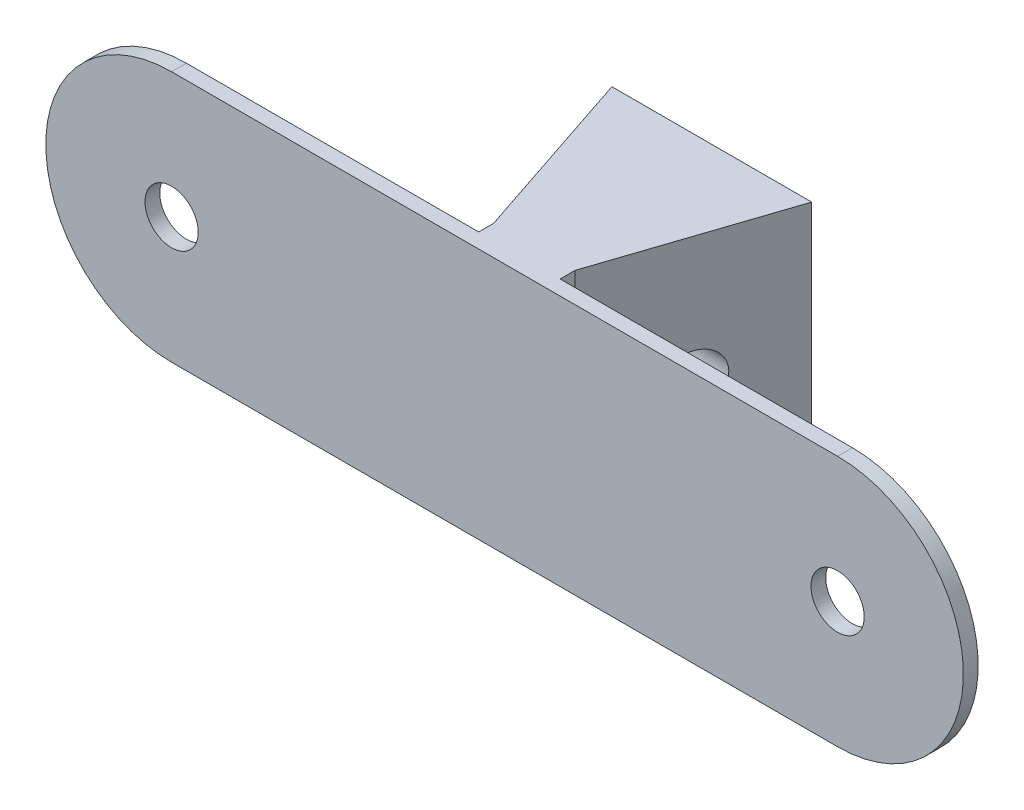
SolidWorks part; units mm, degrees
ref_plane "Front Plane" through (0, 0, 0) normal (0, 0, 1) x (1, 0, 0)
ref_plane "Top Plane" through (0, 0, 0) normal (0, 1, 0) x (1, 0, 0)
ref_plane "Right Plane" through (0, 0, 0) normal (1, 0, 0) x (0, 0, -1)
sketch "Sketch1" plane through (0, 0, 0) normal (0, 0, 1) x (1, 0, 0)
  line L0 (0, 0) -> (45, 0) construction
  line L1 (0, 8.5) -> (45, 8.5)
  line L2 (0, -8.5) -> (45, -8.5)
  arc A0 (0, 8.5) -> (0, -8.5) centre (0, 0) ccw
  arc A1 (45, -8.5) -> (45, 8.5) centre (45, 0) ccw
  point P3 (22.5, 0)
  dimension "D1" = 45
  dimension "D2" = 17
extrude "Boss-Extrude1" add sketch "Sketch1" along normal blind 1
hole_wizard "M3 Clearance Hole1" positions "Sketch2" profile "Sketch3" hole size "M3" standard "ANSI Metric" end condition up to next
sketch "Sketch2" plane through (0, 0, 1) normal (0, 0, 1) x (1, 0, 0)
  point P0 (0, 0)
  point P3 (45, 0)
  dimension "D1" = 45
sketch "Sketch3" plane through (0, 0, 1) normal (1, 0, 0) x (0, -1, 0)
  line L0 (0, 0) -> (0, 1)
  line L1 (0, 1) -> (1.8, 1)
  line L2 (1.8, 1) -> (1.8, 0)
  line L5 (1.8, 0) -> (0, 0)
  line L11 (0, -6.35) -> (0, 107.95) construction
  dimension "Thru Hole Dia." = 3.6
  dimension "Thru Hole Depth" = 1
sketch "Sketch4" plane through (0, 8.5, 0) normal (0, 1, 0) x (1, 0, 0)
  line L5 (19.75, 0) -> (19.75, 1)
  line L6 (45, 0) -> (0, 0) construction
  line L7 (19.75, 1) -> (15.75, 13)
  line L8 (15.75, 13) -> (29.25, 13)
  line L9 (29.25, 13) -> (25.25, 1)
  line L10 (25.25, 1) -> (25.25, 0)
  line L11 (25.25, 0) -> (19.75, 0)
  dimension "D1" = 5.5
  dimension "D2" = 13.5
  dimension "D3" = 4
  dimension "D4" = 13
  dimension "D5" = 12
  dimension "D6" = 12
  dimension "D7" = 19.75
extrude "Boss-Extrude2" add sketch "Sketch4" against normal blind 15.5
hole_wizard "M3 Clearance Hole2" positions "Sketch5" profile "Sketch6" hole size "M3" standard "ANSI Metric" end condition through all
sketch "Sketch5" plane through (0, 0, 0) normal (1, 0, 0) x (0, 0, -1)
  line L0 (1, -7) -> (13, -7) construction
  point P0 (7, 0)
  dimension "D1" = 7
  dimension "D2" = 7
sketch "Sketch6" plane through (0, 0, -7) normal (0, 1, 0) x (0, 0, 1)
  line L0 (0, 0) -> (0, 53.5)
  line L1 (0, 53.5) -> (1.8, 53.5)
  line L2 (1.8, 53.5) -> (1.8, 0)
  line L5 (1.8, 0) -> (0, 0)
  line L11 (0, -6.35) -> (0, 107.95) construction
  dimension "Thru Hole Dia." = 3.6
  dimension "Thru Hole Depth" = 53.5
